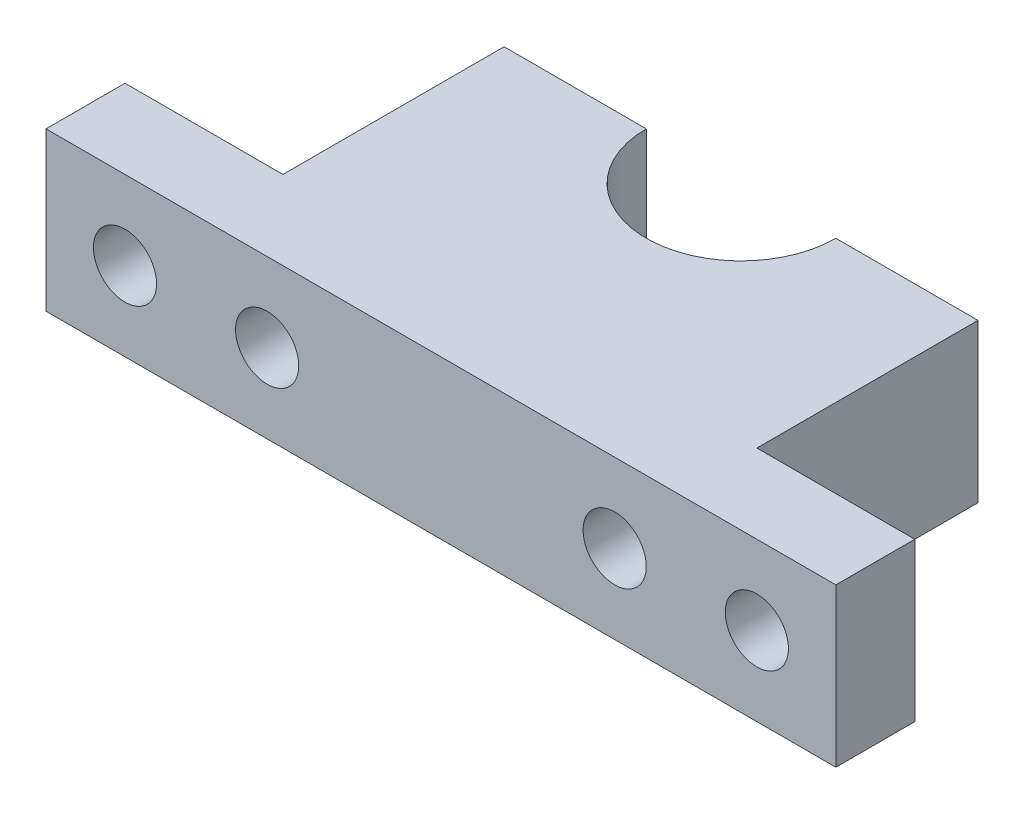
SolidWorks part; units mm, degrees
ref_plane "Front Plane" through (0, 0, 0) normal (0, 0, 1) x (1, 0, 0)
ref_plane "Top Plane" through (0, 0, 0) normal (0, 1, 0) x (1, 0, 0)
ref_plane "Right Plane" through (0, 0, 0) normal (1, 0, 0) x (0, 0, -1)
sketch "Sketch1" plane through (0, 0, 0) normal (0, 1, 0) x (1, 0, 0)
  line L0 (25, 0) -> (-25, 0)
  line L1 (-25, 0) -> (-25, 5)
  line L2 (-25, 5) -> (-15, 5)
  line L3 (-15, 5) -> (-15, 19)
  line L4 (-15, 19) -> (-6, 19)
  line L5 (0, 13) -> (0, 0) construction
  line L6 (15, 5) -> (15, 19)
  line L7 (25, 5) -> (15, 5)
  line L8 (25, 0) -> (25, 5)
  line L9 (6, 19) -> (15, 19)
  arc A0 (-6, 19) -> (6, 19) centre (0, 19) ccw
extrude "Boss-Extrude1" add sketch "Sketch1" along normal blind 10
sketch "Sketch2" plane through (0, 0, 0) normal (0, 0, 1) x (1, 0, 0)
  circle A0 centre (-20, 5) radius 2
  circle A1 centre (-11, 5) radius 2
  circle A2 centre (20, 5) radius 2
  circle A3 centre (11, 5) radius 2
extrude "Cut-Extrude1" cut sketch "Sketch2" against normal through all
